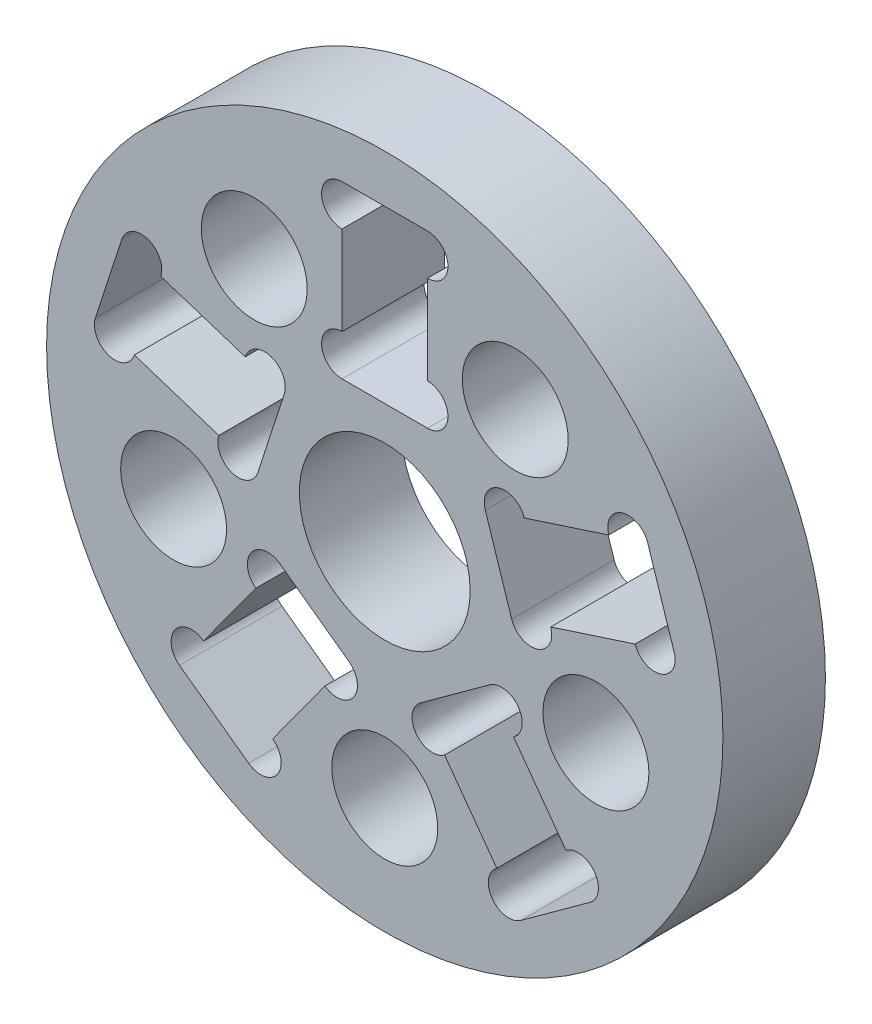
SolidWorks part; units mm, degrees
ref_plane "前视基准面" through (0, 0, 0) normal (0, 0, 1) x (1, 0, 0)
ref_plane "上视基准面" through (0, 0, 0) normal (0, 1, 0) x (1, 0, 0)
ref_plane "右视基准面" through (0, 0, 0) normal (1, 0, 0) x (0, 0, -1)
sketch "草图1" plane through (0, 0, 0) normal (0, 0, 1) x (1, 0, 0)
  circle A0 centre (0, 0) radius 9.9
  dimension "D1" = 19.8
extrude "凸台-拉伸1" add sketch "草图1" along normal mid plane 3
sketch "草图2" plane through (0, 0, 1.5) normal (0, 0, 1) x (1, 0, 0)
  line L1 (1.25, 3.5) -> (-1.25, 3.5)
  line L2 (1.25, 3.5) -> (1.25, 8.5)
  line L3 (1.25, 8.5) -> (-1.25, 8.5)
  line L4 (-1.25, 3.5) -> (-1.25, 8.5)
  line L5 (1.25, 3.5) -> (-1.25, 8.5) construction
  line L6 (1.25, 8.5) -> (-1.25, 3.5) construction
  circle A0 centre (0, -6.5) radius 1.55
  circle A1 centre (0, 0) radius 6.5 construction
  circle A2 centre (0, 0) radius 6 construction
  point P6 (0, 6)
  dimension "D1" = 13
  dimension "D2" = 3.1
  dimension "D5" = 12
  dimension "D3" = 2.5
  dimension "D4" = 5
extrude "切除-拉伸1" cut sketch "草图2" against normal through all
pattern_circular "阵列(圆周)1" count 5 over 360 about axis through (0, 0, 0) along (0, 0, 1) of "切除-拉伸1"
sketch "草图3" plane through (0, 0, 1.5) normal (0, 0, 1) x (1, 0, 0)
  line L0 (1.25, 3.5) -> (1.25, 8.5) construction
  line L1 (-1.25, 8.5) -> (-1.25, 3.5) construction
  circle A0 centre (1.25, 7.9) radius 0.6
  circle A1 centre (-1.25, 7.9) radius 0.6
  circle A2 centre (-1.25, 4.1) radius 0.6
  circle A3 centre (1.25, 4.1) radius 0.6
  dimension "D1" = 1.2
extrude "切除-拉伸2" cut sketch "草图3" against normal through all
pattern_circular "阵列(圆周)2" count 5 over 360 about axis through (0, 0, 0) along (0, 0, 1) of "切除-拉伸2"
sketch "草图4" plane through (0, 0, 1.5) normal (0, 0, 1) x (1, 0, 0)
  circle A0 centre (0, 0) radius 2.5
  dimension "D1" = 5
extrude "切除-拉伸3" cut sketch "草图4" against normal through all
